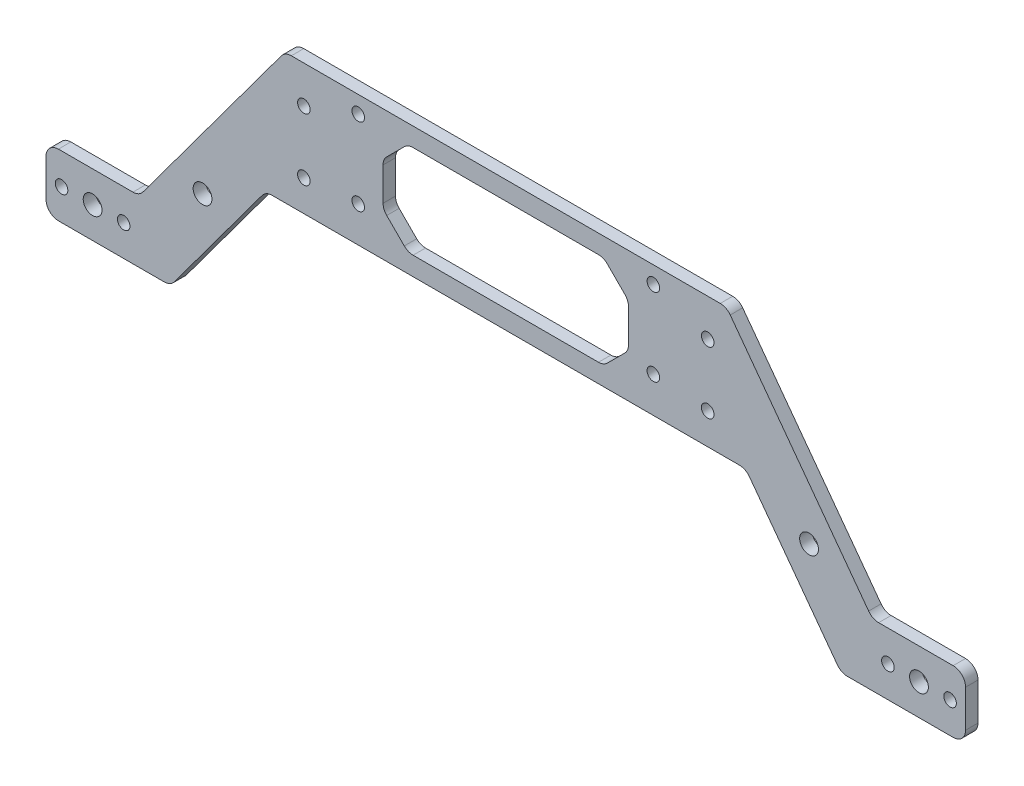
SolidWorks part; units mm, degrees
material "Thornel Mat VMA"
ref_plane "前视基准面" through (0, 0, 0) normal (0, 0, 1) x (1, 0, 0)
ref_plane "上视基准面" through (0, 0, 0) normal (0, 1, 0) x (1, 0, 0)
ref_plane "右视基准面" through (0, 0, 0) normal (1, 0, 0) x (0, 0, -1)
other "Configuration Table"
sketch "草图1" plane through (0, 0, 0) normal (0, 0, 1) x (1, 0, 0)
  line L0 (-143, -51.5) -> (-133, -51.5) construction
  line L1 (-65, -10) -> (65, -10) construction
  line L2 (-65, -10) -> (-65, 10) construction
  line L3 (-65, 10) -> (65, 10) construction
  line L4 (65, -10) -> (65, 10) construction
  line L5 (-65, -10) -> (65, 10) construction
  line L6 (-65, 10) -> (65, -10) construction
  line L7 (-133, -51.5) -> (-123, -51.5) construction
  line L8 (0, 0) -> (0, -50000) construction
  line L9 (-118, -61.5) -> (-107.9142, -61.5)
  line L10 (-148, -61.5) -> (-118, -61.5)
  line L11 (-148, -61.5) -> (-148, -41.5)
  line L12 (-148, -41.5) -> (-118, -41.5)
  line L13 (-118, -61.5) -> (-118, -41.5)
  line L14 (-148, -61.5) -> (-118, -41.5) construction
  line L15 (-148, -41.5) -> (-118, -61.5) construction
  line L16 (-77.2313, -20) -> (77.2313, -20)
  line L17 (-118, -41.5) -> (-71.0515, 22)
  line L18 (-71.0515, 22) -> (71.0515, 22)
  line L19 (-107.9142, -61.5) -> (-77.2313, -20)
  line L20 (-47.5, -8.5) -> (47.5, -8.5) construction
  line L21 (-47.5, -8.5) -> (-47.5, 16.5) construction
  line L22 (-47.5, 16.5) -> (47.5, 16.5) construction
  line L23 (47.5, -8.5) -> (47.5, 16.5) construction
  line L24 (-47.5, -8.5) -> (47.5, 16.5) construction
  line L25 (-47.5, 16.5) -> (47.5, -8.5) construction
  line L26 (148, -41.5) -> (118, -61.5) construction
  line L27 (148, -61.5) -> (118, -41.5) construction
  line L28 (133, -51.5) -> (123, -51.5) construction
  line L29 (143, -51.5) -> (133, -51.5) construction
  line L30 (118, -61.5) -> (118, -41.5)
  line L31 (148, -41.5) -> (118, -41.5)
  line L32 (148, -61.5) -> (148, -41.5)
  line L33 (148, -61.5) -> (118, -61.5)
  line L34 (118, -61.5) -> (107.9142, -61.5)
  line L35 (118, -41.5) -> (71.0515, 22)
  line L36 (107.9142, -61.5) -> (77.2313, -20)
  line L37 (-118, -41.5) -> (-107.9142, -61.5) construction
  line L38 (-77.2313, -20) -> (-87.3171, 0) construction
  line L39 (-82.2742, -10) -> (-112.9571, -51.5) construction
  circle A4 centre (-65, 10) radius 2.025
  circle A5 centre (-65, -10) radius 2.025
  circle A6 centre (65, 10) radius 2.025
  circle A7 centre (65, -10) radius 2.025
  circle A8 centre (-143, -51.5) radius 2.025
  circle A9 centre (-123, -51.5) radius 2.025
  circle A10 centre (-133, -51.5) radius 3.025
  circle A11 centre (143, -51.5) radius 2.025
  circle A12 centre (133, -51.5) radius 3.025
  circle A13 centre (123, -51.5) radius 2.025
  circle A14 centre (-47.5, 16.5) radius 2.025
  circle A15 centre (-47.5, -8.5) radius 2.025
  circle A16 centre (47.5, 16.5) radius 2.025
  circle A17 centre (47.5, -8.5) radius 2.025
  circle A18 centre (-65, 10) radius 12 construction
  circle A19 centre (133, -51.5) radius 3.025
  circle A20 centre (123, -51.5) radius 2.025
  circle A21 centre (143, -51.5) radius 2.025
  circle A22 centre (-97.6157, -30.75) radius 3.025
  circle A23 centre (97.6157, -30.75) radius 3.025
  point P0 (0, 0)
  point P29 (0, 22)
  point P31 (0, 4)
  point P54 (0, -20)
  dimension "D1" = 130
  dimension "D3" = 4.05
  dimension "D5" = 6.05
  dimension "D6" = 58
  dimension "D7" = 41.5
  dimension "D8" = 5
  dimension "D10" = 10
  dimension "D16" = 6.05
  dimension "D2" = 20
  dimension "D4" = 20
  dimension "D9" = 20
  dimension "D11" = 25
  dimension "D12" = 95
  dimension "D13" = 78
  dimension "D14" = 20
  dimension "D15" = 12
extrude "凸台-拉伸1" add sketch "草图1" along normal blind 4 contours L10 L13 L12 L11 A10 A9 A8 | L36 L34 L30 L35 L18 L17 L13 L9 L19 L16 A17 A16 A15 A14 A7 A6 A5 A4 | L33 L32 L31 L30 A12 A11 A13
sketch "草图2" plane through (0, 0, 4) normal (0, 0, 1) x (1, 0, 0)
  line L0 (0, 0) -> (0, 1) construction
  line L1 (47.5, -8.5) -> (-47.5, -8.5) construction
  line L2 (47.5, -8.5) -> (47.5, 16.5) construction
  line L3 (47.5, 16.5) -> (-47.5, 16.5) construction
  line L4 (-47.5, -8.5) -> (-47.5, 16.5) construction
  line L5 (-71.0515, 22) -> (71.0515, 22) construction
  line L7 (-39.5, -14) -> (39.5, -14)
  line L8 (-39.5, -14) -> (-39.5, 16)
  line L9 (-39.5, 16) -> (39.5, 16)
  line L10 (39.5, -14) -> (39.5, 16)
  line L11 (-39.5, -14) -> (39.5, 16) construction
  line L12 (-39.5, 16) -> (39.5, -14) construction
  point P0 (0, 1)
  point P10 (0, 1)
  dimension "D1" = 8
  dimension "D2" = 6
  dimension "D3" = 30
extrude "切除-拉伸1" cut sketch "草图2" against normal blind 4
fillet "圆角1" radius 4 12 edges at (-148, -61.5, 2) (-148, -41.5, 2) (-118, -41.5, 2) (-71.0515, 22, 2) (118, -41.5, 2) (148, -41.5, 2) (148, -61.5, 2) (107.9142, -61.5, 2) (77.2313, -20, 2) (-77.2313, -20, 2) (-107.9142, -61.5, 2) (71.0515, 22, 2)
chamfer "倒角1" distance 8 angle 45 4 edges at (39.5, -14, 2) (39.5, 16, 2) (-39.5, 16, 2) (-39.5, -14, 2)
fillet "圆角2" radius 4 8 edges at (39.5, 8, 2) (31.5, 16, 2) (-31.5, 16, 2) (-39.5, 8, 2) (-39.5, -6, 2) (-31.5, -14, 2) (39.5, -6, 2) (31.5, -14, 2)
